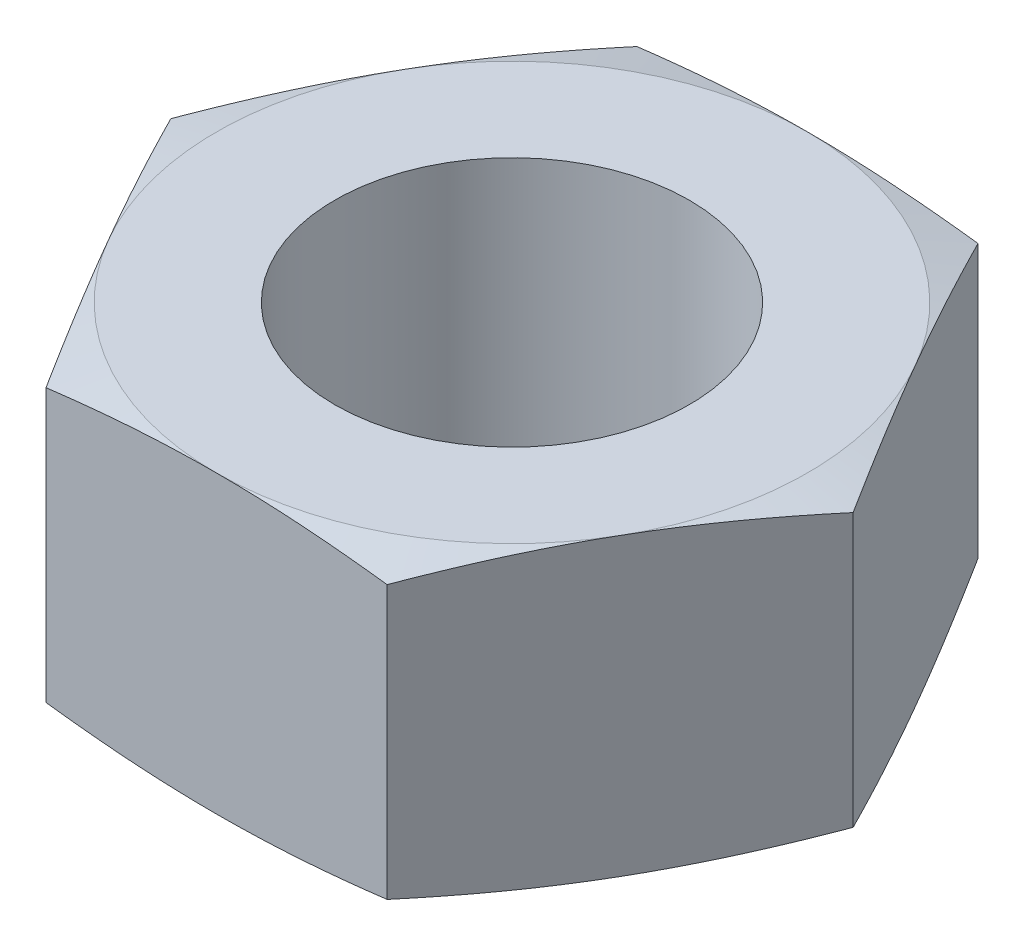
SolidWorks part; units mm, degrees
ref_plane "Front Plane" through (0, 0, 0) normal (0, 0, 1) x (1, 0, 0)
ref_plane "Top Plane" through (0, 0, 0) normal (0, 1, 0) x (1, 0, 0)
ref_plane "Right Plane" through (0, 0, 0) normal (1, 0, 0) x (0, 0, -1)
sketch "Sketch1" plane through (0, 0, 0) normal (0, 1, 0) x (1, 0, 0)
  line L1 (5.7735, 0) -> (2.8868, 5)
  line L2 (2.8868, 5) -> (-2.8868, 5)
  line L3 (-2.8868, 5) -> (-5.7735, 0)
  line L4 (-5.7735, 0) -> (-2.8868, -5)
  line L5 (-2.8868, -5) -> (2.8868, -5)
  line L6 (2.8868, -5) -> (5.7735, 0)
  circle A0 centre (0, 0) radius 3
extrude "Boss-Extrude1" add sketch "Sketch1" along normal blind 5
sketch "Sketch2" plane through (0, 5, 0) normal (0, 1, 0) x (1, 0, 0)
  circle A0 centre (0, 0) radius 5
extrude "Cut-Extrude2" cut sketch "Sketch2" against normal blind 0.2 draft 76 flip side to cut
sketch "Sketch3" plane through (0, 0, 0) normal (0, -1, 0) x (1, 0, 0)
  circle A0 centre (0, 0) radius 5
extrude "Cut-Extrude3" cut sketch "Sketch3" against normal blind 0.2 draft 76 flip side to cut
